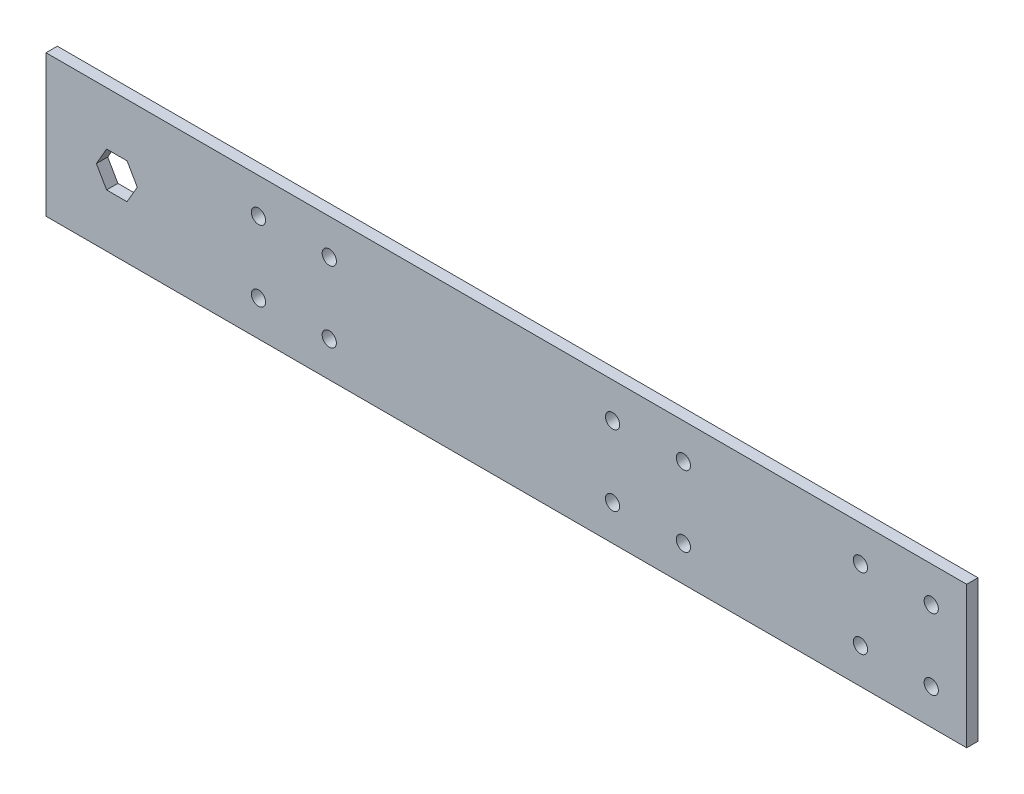
SolidWorks part; units mm, degrees
material "6061-T6 (SS)"
ref_plane "Front Plane" through (0, 0, 0) normal (0, 0, 1) x (1, 0, 0)
ref_plane "Top Plane" through (0, 0, 0) normal (0, 1, 0) x (1, 0, 0)
ref_plane "Right Plane" through (0, 0, 0) normal (1, 0, 0) x (0, 0, -1)
sketch "Sketch1" plane through (0, 0, 0) normal (0, 0, 1) x (1, 0, 0)
  line L1 (0, 0) -> (330.2, 0)
  line L2 (0, 0) -> (0, 50.8)
  line L3 (0, 50.8) -> (330.2, 50.8)
  line L4 (330.2, 0) -> (330.2, 50.8)
  dimension "D1" = 50.8
  dimension "D2" = 330.2
extrude "base" add sketch "Sketch1" along normal blind 4.064
hole_wizard "#10 Clearance Hole - basket mount" positions "Sketch6" profile "Sketch5" hole size "#10" standard "ANSI Inch" end condition through all
sketch "Sketch6" plane through (0, 0, 4.064) normal (0, 0, 1) x (1, 0, 0)
  line L1 (203.2, 12.7) -> (228.6, 12.7) construction
  line L2 (203.2, 12.7) -> (203.2, 38.1) construction
  line L3 (203.2, 38.1) -> (228.6, 38.1) construction
  line L4 (228.6, 12.7) -> (228.6, 38.1) construction
  line L5 (203.2, 38.1) -> (203.2, 50.8) construction
  line L6 (330.2, 50.8) -> (0, 50.8) construction
  line L8 (203.2, 12.7) -> (203.2, 0) construction
  line L9 (0, 0) -> (330.2, 0) construction
  line L12 (76.2, 38.1) -> (101.6, 38.1) construction
  line L13 (76.2, 38.1) -> (76.2, 12.7) construction
  line L14 (76.2, 12.7) -> (101.6, 12.7) construction
  line L15 (101.6, 38.1) -> (101.6, 12.7) construction
  line L16 (0, 50.8) -> (0, 0) construction
  line L17 (88.9, 38.1) -> (88.9, 50.8) construction
  line L20 (88.9, 12.7) -> (88.9, 0) construction
  point P1 (203.2, 12.7)
  point P2 (228.6, 38.1)
  point P63 (203.2, 38.1)
  point P64 (228.6, 12.7)
  point P87 (76.2, 38.1)
  point P88 (101.6, 12.7)
  point P177 (76.2, 12.7)
  point P178 (101.6, 38.1)
  dimension "D1" = 25.4
  dimension "D2" = 25.4
  dimension "D3" = 25.4
  dimension "D4" = 25.4
  dimension "D5" = 76.2
  dimension "D6" = 101.6
sketch "Sketch5" plane through (203.2, 12.7, 4.064) normal (1, 0, 0) x (0, -1, 0)
  line L0 (0, 0) -> (0, 4.064)
  line L1 (0, 4.064) -> (2.5527, 4.064)
  line L2 (2.5527, 4.064) -> (2.5527, 0)
  line L5 (2.5527, 0) -> (0, 0)
  line L11 (0, -6.35) -> (0, 107.95) construction
  dimension "Thru Hole Dia." = 5.1054
  dimension "Thru Hole Depth" = 4.064
sketch "Sketch7" plane through (0, 0, 4.064) normal (0, 0, 1) x (1, 0, 0)
  line L0 (25.4, 50.8) -> (25.4, 25.4) construction
  line L1 (330.2, 50.8) -> (0, 50.8) construction
  line L2 (25.4, 25.4) -> (25.4, 0) construction
  line L3 (0, 0) -> (330.2, 0) construction
  line L5 (0, 50.8) -> (0, 0) construction
  line L7 (21.7338, 31.75) -> (18.0677, 25.4)
  line L8 (18.0677, 25.4) -> (21.7338, 19.05)
  line L9 (21.7338, 19.05) -> (29.0662, 19.05)
  line L10 (29.0662, 19.05) -> (32.7323, 25.4)
  line L11 (32.7323, 25.4) -> (29.0662, 31.75)
  line L12 (29.0662, 31.75) -> (21.7338, 31.75)
  circle A0 centre (25.4, 25.4) radius 6.35 construction
  dimension "D1" = 12.7
  dimension "D2" = 25.4
extrude "pivot hole" cut sketch "Sketch7" against normal through all
hole_wizard "#10 Clearance Hole1" positions "Sketch9" profile "Sketch8" hole size "#10" standard "ANSI Inch" end condition through all
sketch "Sketch9" plane through (0, 0, 4.064) normal (0, 0, 1) x (1, 0, 0)
  line L1 (317.5, 38.1) -> (292.1, 38.1) construction
  line L2 (317.5, 38.1) -> (317.5, 12.7) construction
  line L3 (317.5, 12.7) -> (292.1, 12.7) construction
  line L4 (292.1, 38.1) -> (292.1, 12.7) construction
  line L5 (330.2, 0) -> (330.2, 50.8) construction
  line L6 (317.5, 38.1) -> (317.5, 50.8) construction
  line L7 (330.2, 50.8) -> (0, 50.8) construction
  line L10 (317.5, 12.7) -> (317.5, 0) construction
  line L11 (0, 0) -> (330.2, 0) construction
  point P1 (317.5, 38.1)
  point P2 (292.1, 12.7)
  point P53 (317.5, 12.7)
  point P54 (292.1, 38.1)
  dimension "D1" = 25.4
  dimension "D2" = 25.4
  dimension "D3" = 12.7
sketch "Sketch8" plane through (317.5, 38.1, 4.064) normal (1, 0, 0) x (0, -1, 0)
  line L0 (0, 0) -> (0, 4.064)
  line L1 (0, 4.064) -> (2.5527, 4.064)
  line L2 (2.5527, 4.064) -> (2.5527, 0)
  line L5 (2.5527, 0) -> (0, 0)
  line L11 (0, -6.35) -> (0, 107.95) construction
  dimension "Thru Hole Dia." = 5.1054
  dimension "Thru Hole Depth" = 4.064
